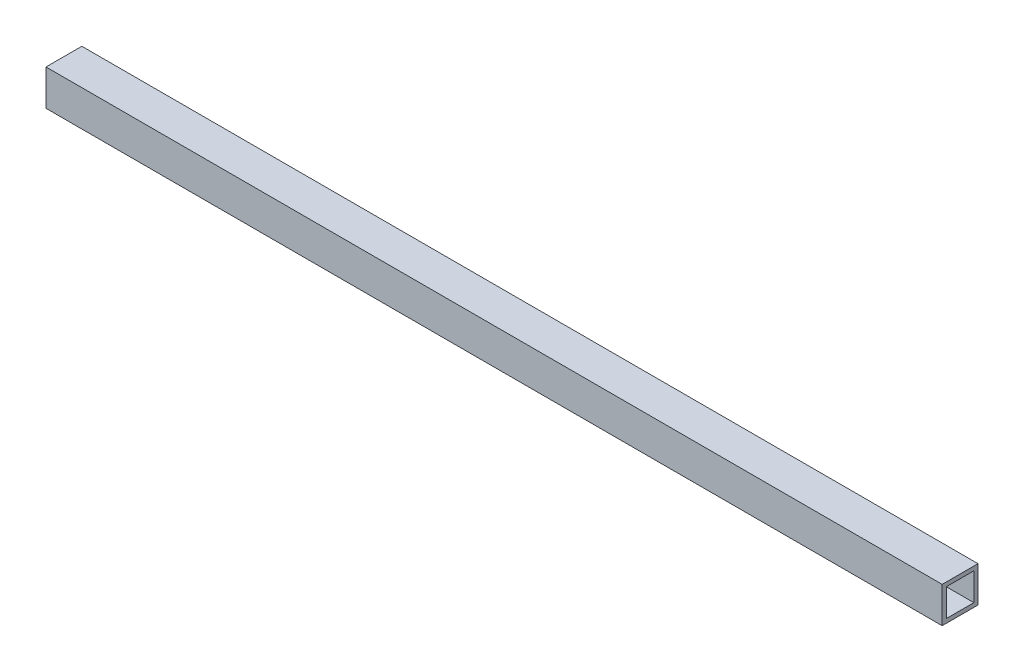
SolidWorks part; units mm, degrees
ref_plane "Front Plane" through (0, 0, 0) normal (0, 0, 1) x (1, 0, 0)
ref_plane "Top Plane" through (0, 0, 0) normal (0, 1, 0) x (1, 0, 0)
ref_plane "Right Plane" through (0, 0, 0) normal (1, 0, 0) x (0, 0, -1)
sketch "Sketch1" plane through (0, 0, 0) normal (0, 1, 0) x (1, 0, 0)
  line L1 (-325, 13) -> (325, 13)
  line L2 (-325, 13) -> (-325, -13)
  line L3 (-325, -13) -> (325, -13)
  line L4 (325, 13) -> (325, -13)
  line L5 (-325, 13) -> (325, -13) construction
  line L6 (-325, -13) -> (325, 13) construction
  point P0 (0, 0)
  dimension "D1" = 26
  dimension "D2" = 650
extrude "Boss-Extrude1" add sketch "Sketch1" along normal blind 26
shell "Shell1" thickness 3
